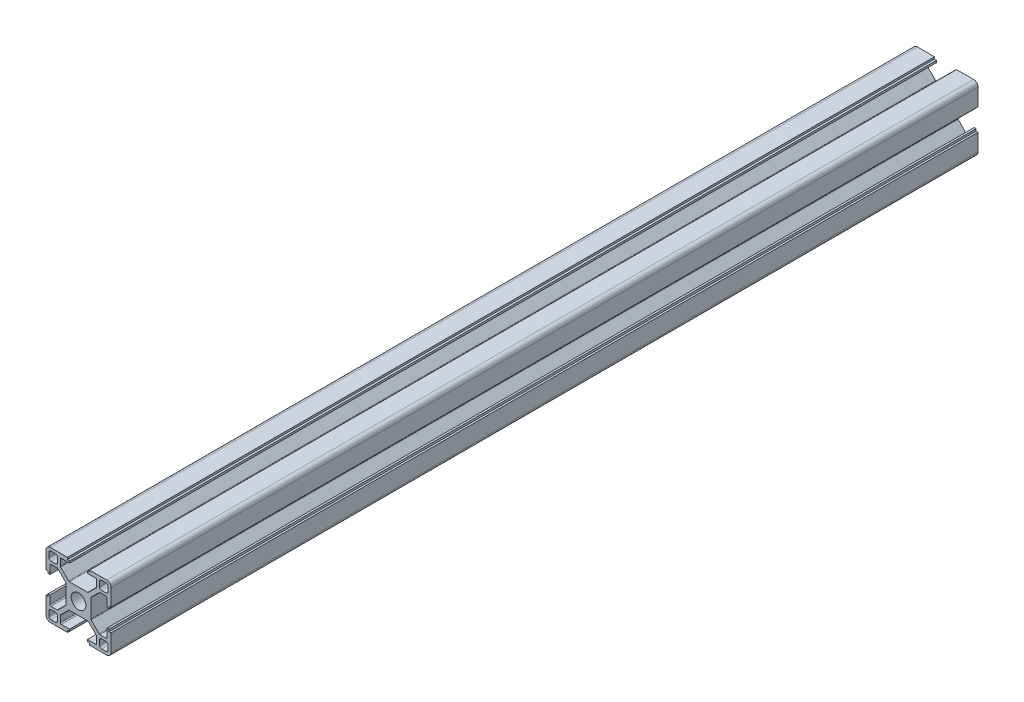
SolidWorks part; units mm, degrees
ref_plane "前视基准面" through (0, 0, 0) normal (0, 0, 1) x (1, 0, 0)
ref_plane "上视基准面" through (0, 0, 0) normal (0, 1, 0) x (1, 0, 0)
ref_plane "右视基准面" through (0, 0, 0) normal (1, 0, 0) x (0, 0, -1)
sketch "草图1" plane through (0, 0, 0) normal (0, 0, 1) x (1, 0, 0)
  line L0 (0, 0) -> (0, 65.3905) construction
  line L1 (0, 0) -> (64.2648, 0) construction
  line L2 (0, 0) -> (79.9729, 79.9729) construction
  line L3 (5.7, 0) -> (5.7, 4.4272)
  line L4 (5.7, 4.4272) -> (9.6728, 8.4)
  line L5 (9.6728, 8.4) -> (13.2, 8.4)
  line L6 (13.2, 8.4) -> (13.2, 4.1)
  line L7 (13.2, 4.1) -> (14.1, 4.1)
  line L8 (14.1, 4.1) -> (14.1, 5.1)
  line L9 (14.1, 5.1) -> (15, 5.1)
  line L10 (15, 5.1) -> (15, 15)
  line L11 (5.1, 15) -> (15, 15)
  line L12 (5.1, 14.1) -> (5.1, 15)
  line L13 (4.1, 14.1) -> (5.1, 14.1)
  line L14 (4.1, 13.2) -> (4.1, 14.1)
  line L15 (8.4, 13.2) -> (4.1, 13.2)
  line L16 (8.4, 9.6728) -> (8.4, 13.2)
  line L17 (4.4272, 5.7) -> (8.4, 9.6728)
  line L18 (0, 5.7) -> (4.4272, 5.7)
  line L20 (9.7, 9.7) -> (13.7, 9.7)
  line L21 (9.7, 9.7) -> (9.7, 13.7)
  line L22 (9.7, 13.7) -> (13.7, 13.7)
  line L23 (13.7, 9.7) -> (13.7, 13.7)
  line L24 (9.7, 9.7) -> (13.7, 13.7) construction
  line L25 (9.7, 13.7) -> (13.7, 9.7) construction
  line L26 (0, 5.7) -> (0, 0)
  line L27 (0, 0) -> (5.7, 0)
  point P9 (11.7, 11.7)
  dimension "D1" = 45
  dimension "D2" = 5.7
  dimension "D3" = 1.8
  dimension "D4" = 0.9
  dimension "D5" = 8.2
  dimension "D6" = 10.2
  dimension "D7" = 1.8
  dimension "D8" = 15
  dimension "D9" = 16.8
  dimension "D10" = 4
  dimension "D11" = 1.3
extrude "凸台-拉伸1" add sketch "草图1" along normal blind 400 contours L3 L4 L5 L6 L7 L8 L9 L10 L11 L12 L13 L14 L15 L16 L17 L18 L26 L27
fillet "圆角1" radius 1 4 edges at (9.7, 9.7, 200) (13.7, 9.7, 200) (9.7, 13.7, 200) (13.7, 13.7, 200)
fillet "圆角2" radius 2 1 edges at (15, 15, 200)
fillet "圆角3" radius 0.5 6 edges at (5.7, 4.4272, 200) (4.4272, 5.7, 200) (8.4, 13.2, 200) (8.4, 9.6728, 200) (9.6728, 8.4, 200) (13.2, 8.4, 200)
pattern_circular "阵列(圆周)1" count 4 over 360 about axis through (0, 0, 0) along (0, 0, 1) of "圆角2", "圆角3", "凸台-拉伸1", "圆角1"
sketch "草图2" plane through (0, 0, 400) normal (0, 0, 1) x (1, 0, 0)
  circle A0 centre (0, 0) radius 3.4
  dimension "D1" = 6.8
extrude "切除-拉伸1" cut sketch "草图2" against normal through all
sketch "草图3" plane through (0, 0, 0) normal (0, 1, 0) x (1, 0, 0)
  line L0 (0, 68.2106) -> (0, -452.0487) construction
  line L1 (4.2201, 0) -> (-4.2201, 0) construction
  line L2 (4.2201, -400) -> (-4.2201, -400) construction
  circle A0 centre (0, -50) radius 3.25
  circle A1 centre (0, -350) radius 3.25
  dimension "D1" = 6.5
  dimension "D3" = 50
  dimension "D2" = 50
extrude "切除-拉伸2" cut sketch "草图3" against normal mid plane 20
